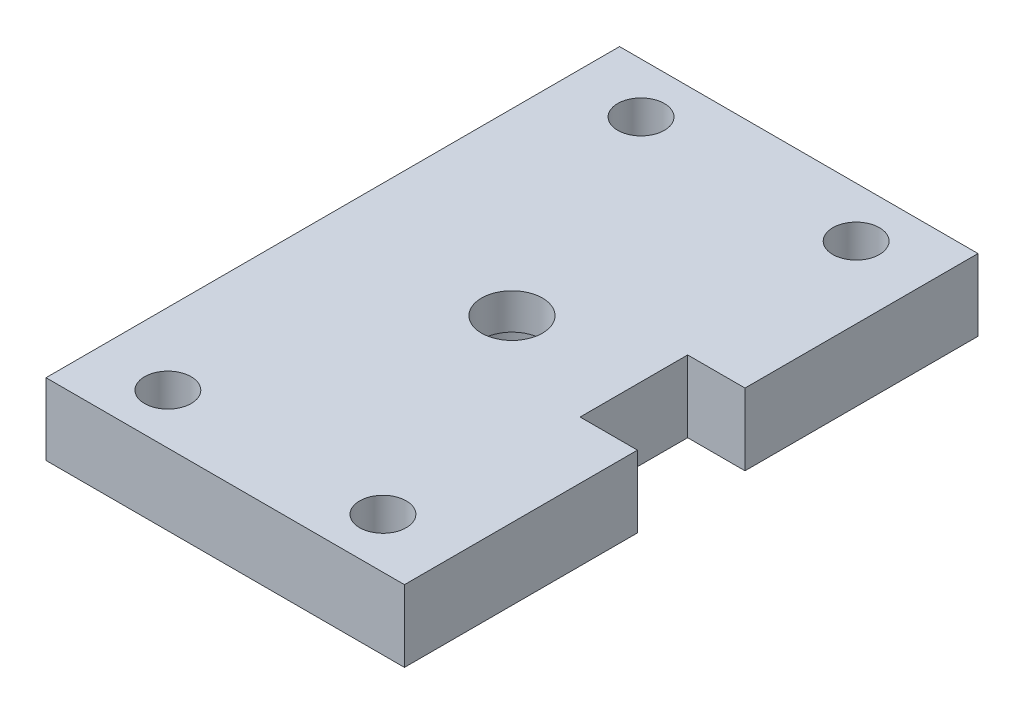
SolidWorks part; units mm, degrees
ref_plane "Front Plane" through (0, 0, 0) normal (0, 0, 1) x (1, 0, 0)
ref_plane "Top Plane" through (0, 0, 0) normal (0, 1, 0) x (1, 0, 0)
ref_plane "Right Plane" through (0, 0, 0) normal (1, 0, 0) x (0, 0, -1)
sketch "Sketch1" plane through (0, 0, 0) normal (0, 1, 0) x (1, 0, 0)
  line L0 (30.8021, -28.7414) -> (-19.1979, -28.7414) construction
  line L5 (-19.0216, -6.7414) -> (30.8021, -6.7414) construction
  line L6 (-19.1097, -46.7414) -> (30.8903, -46.7414)
  line L7 (30.8021, 15.2586) -> (-19.0216, 15.2586) construction
  line L8 (30.8021, 15.2586) -> (30.8021, -28.7414) construction
  line L9 (30.8021, -28.7414) -> (-19.0216, -28.7414) construction
  line L10 (-19.0216, 15.2586) -> (-19.0216, -28.7414) construction
  line L11 (-19.0216, 15.2586) -> (30.8021, -28.7414) construction
  line L12 (-19.0216, -28.7414) -> (30.8021, 15.2586) construction
  line L13 (-19.1097, -46.7414) -> (-19.1097, 33.2586)
  line L14 (-19.1097, 33.2586) -> (30.8903, 33.2586)
  line L15 (30.8903, -46.7414) -> (30.8903, 33.2586)
  line L16 (-19.1097, -46.7414) -> (30.8903, 33.2586) construction
  line L17 (-19.1097, 33.2586) -> (30.8903, -46.7414) construction
  point P0 (0, 0)
  point P1 (5.8903, -6.7414)
  dimension "D1" = 80
  dimension "D2" = 50
extrude "Boss-Extrude1" add sketch "Sketch1" along normal blind 10
sketch "Sketch2" plane through (0, 0, 0) normal (0, -1, 0) x (1, 0, 0)
  line L0 (5.8903, -33.2586) -> (5.8903, 46.7414) construction
  line L1 (30.8903, -33.2586) -> (-19.1097, -33.2586) construction
  line L2 (-19.1097, 46.7414) -> (30.8903, 46.7414) construction
  circle A0 centre (5.8903, 6.7414) radius 4.25
  dimension "D1" = 8.5
extrude "Cut-Extrude1" cut sketch "Sketch2" against normal up to next
sketch "Sketch5" plane through (0, 10, 0) normal (0, 1, 0) x (1, 0, 0)
  line L0 (-19.1097, -39.7414) -> (30.8903, -39.7414) construction
  line L1 (-19.1097, 33.2586) -> (-19.1097, -46.7414) construction
  line L2 (30.8903, -46.7414) -> (30.8903, 33.2586) construction
  line L3 (-19.1097, 26.2586) -> (30.8903, 26.2586) construction
  line L4 (-19.1097, -46.7414) -> (30.8903, -46.7414) construction
  line L5 (30.8903, 33.2586) -> (-19.1097, 33.2586) construction
  circle A0 centre (-9.1097, -39.7414) radius 3.25
  circle A1 centre (20.8903, -39.7414) radius 3.25
  circle A2 centre (-9.1097, 26.2586) radius 3.25
  circle A3 centre (20.8903, 26.2586) radius 3.25
  dimension "D3" = 6.5
  dimension "D4" = 6.5
  dimension "D5" = 6.5
  dimension "D6" = 6.5
  dimension "D1" = 7
  dimension "D2" = 7
  dimension "D7" = 10
  dimension "D8" = 10
  dimension "D9" = 10
  dimension "D10" = 10
extrude "Cut-Extrude3" cut sketch "Sketch5" against normal up to next
sketch "Sketch7" plane through (0, 0, 0) normal (0, -1, 0) x (1, 0, 0)
  circle A0 centre (5.8903, 6.7414) radius 7.5
  dimension "D1" = 15
extrude "Cut-Extrude4" cut sketch "Sketch7" against normal blind 5
sketch "Sketch10" plane through (0, 10, 0) normal (0, 1, 0) x (1, 0, 0)
  line L0 (30.8903, -6.7414) -> (22.3618, -6.7414) construction
  line L2 (30.8903, -46.7414) -> (30.8903, 33.2586) construction
  line L4 (22.8903, -14.2414) -> (30.8903, -14.2414)
  line L5 (22.8903, -14.2414) -> (22.8903, 0.7586)
  line L6 (22.8903, 0.7586) -> (30.8903, 0.7586)
  line L7 (30.8903, -14.2414) -> (30.8903, 0.7586)
  point P10 (22.8903, -6.7414)
  point P11 (0, 0)
  dimension "D1" = 8
  dimension "D2" = 15
extrude "Cut-Extrude5" cut sketch "Sketch10" against normal through all
